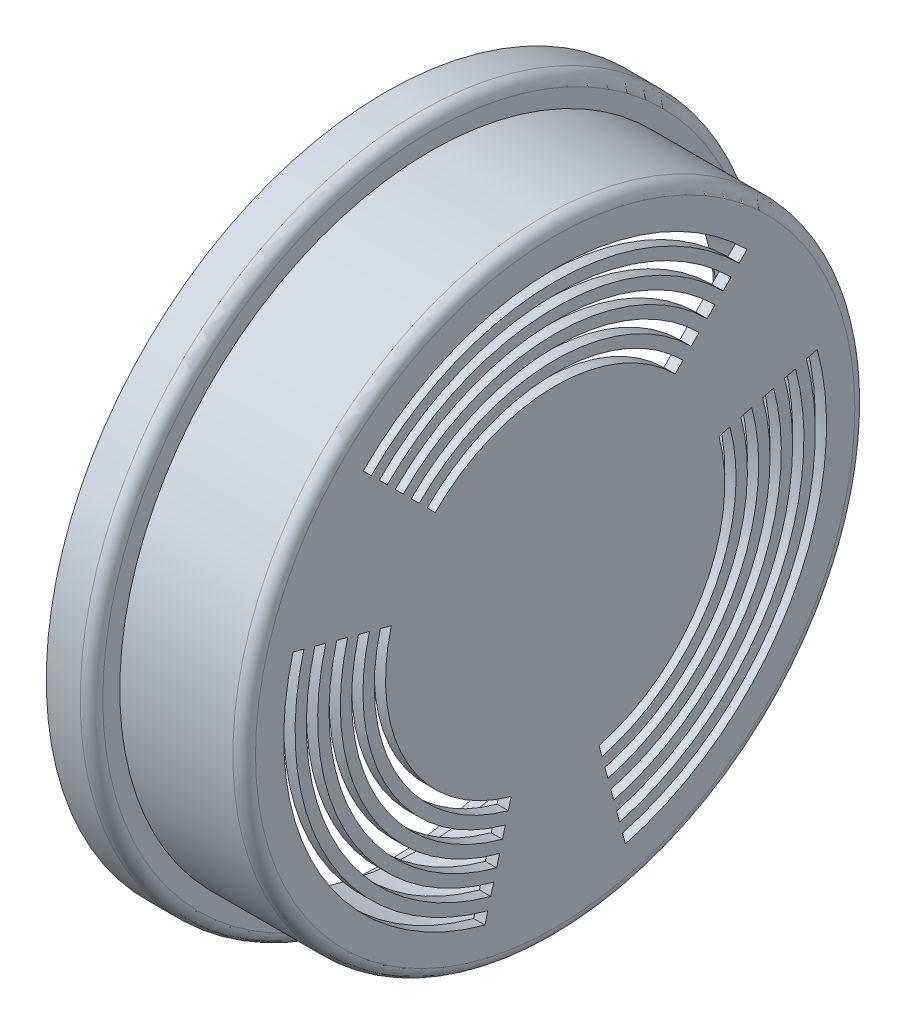
SolidWorks part; units mm, degrees
ref_plane "Front Plane" through (0, 0, 0) normal (0, 0, 1) x (1, 0, 0)
ref_plane "Top Plane" through (0, 0, 0) normal (0, 1, 0) x (1, 0, 0)
ref_plane "Right Plane" through (0, 0, 0) normal (1, 0, 0) x (0, 0, -1)
sketch "Sketch1" plane through (0, 0, 0) normal (0, 0, 1) x (1, 0, 0)
  line L0 (-15, 0) -> (15, 0) construction
  line L1 (-15, 60) -> (-7, 60)
  line L2 (-7, 60) -> (-7, 55)
  line L3 (-7, 55) -> (15, 55)
  line L4 (15, 55) -> (15, 0)
  line L5 (-15, 58) -> (-9, 58)
  line L6 (-9, 58) -> (-9, 53)
  line L7 (-9, 53) -> (13, 53)
  line L8 (13, 53) -> (13, 0)
  line L9 (-15, 58) -> (-15, 60)
  line L10 (13, 0) -> (15, 0)
  point P4 (0, 0)
  dimension "D1" = 8
  dimension "D2" = 120
  dimension "D3" = 30
  dimension "D4" = 5
  dimension "D5" = 2
revolve "Revolve2" add sketch "Sketch1" angle 360 about L0
fillet "Fillet1" radius 2 2 edges at (15, -55, 0) (-9, -58, 0)
fillet "Fillet2" radius 2 1 edges at (-7, -60, 0)
sketch "Sketch2" plane through (15, 0, 0) normal (1, 0, 0) x (0, 0, -1)
  line L0 (0, 0) -> (0, 67.6029) construction
  line L1 (0, 0) -> (-33.9411, 33.9411)
  line L2 (0, 0) -> (33.9411, 33.9411)
  arc A0 (33.9411, 33.9411) -> (-33.9411, 33.9411) centre (0, 0) ccw
  circle A1 centre (0, 0) radius 53
  circle A2 centre (0, 0) radius 53
  arc A3 (32.5269, 32.5269) -> (-32.5269, 32.5269) centre (0, 0) ccw
  arc A4 (31.1127, 31.1127) -> (-31.1127, 31.1127) centre (0, 0) ccw
  arc A5 (29.6985, 29.6985) -> (-29.6985, 29.6985) centre (0, 0) ccw
  arc A6 (28.2843, 28.2843) -> (-28.2843, 28.2843) centre (0, 0) ccw
  arc A7 (26.8701, 26.8701) -> (-26.8701, 26.8701) centre (0, 0) ccw
  arc A8 (-25.4558, 25.4558) -> (25.4558, 25.4558) centre (0, 0) cw
  arc A9 (-24.0416, 24.0416) -> (24.0416, 24.0416) centre (0, 0) cw
  arc A10 (-22.6274, 22.6274) -> (22.6274, 22.6274) centre (0, 0) cw
  arc A11 (-21.2132, 21.2132) -> (21.2132, 21.2132) centre (0, 0) cw
  dimension "D2" = 106
  dimension "D3" = 5
  dimension "D4" = 2
  dimension "D5" = 2
  dimension "D6" = 2
  dimension "D7" = 2
  dimension "D8" = 2
  dimension "D11" = 2
  dimension "D12" = 2
  dimension "D13" = 2
  dimension "D14" = 2
  dimension "D9" = 45
  dimension "D10" = 90
  dimension "D1" = 0
extrude "Cut-Extrude2" cut sketch "Sketch2" against normal up to next (2 mm away) contours A3 L0 A0 L1 | L0 A3 L2 A0 | A5 L0 A4 L1 | L0 A5 L2 A4 | A7 L0 A6 L1 | L0 A7 L2 A6 | A9 L0 A8 L1 | L0 A9 L2 A8 | A11 L0 A10 L1 | L0 A11 L2 A10
pattern_circular "CirPattern1" count 3 over 360 about axis through (0, 0, 0) along (1, 0, 0) of "Cut-Extrude2"
